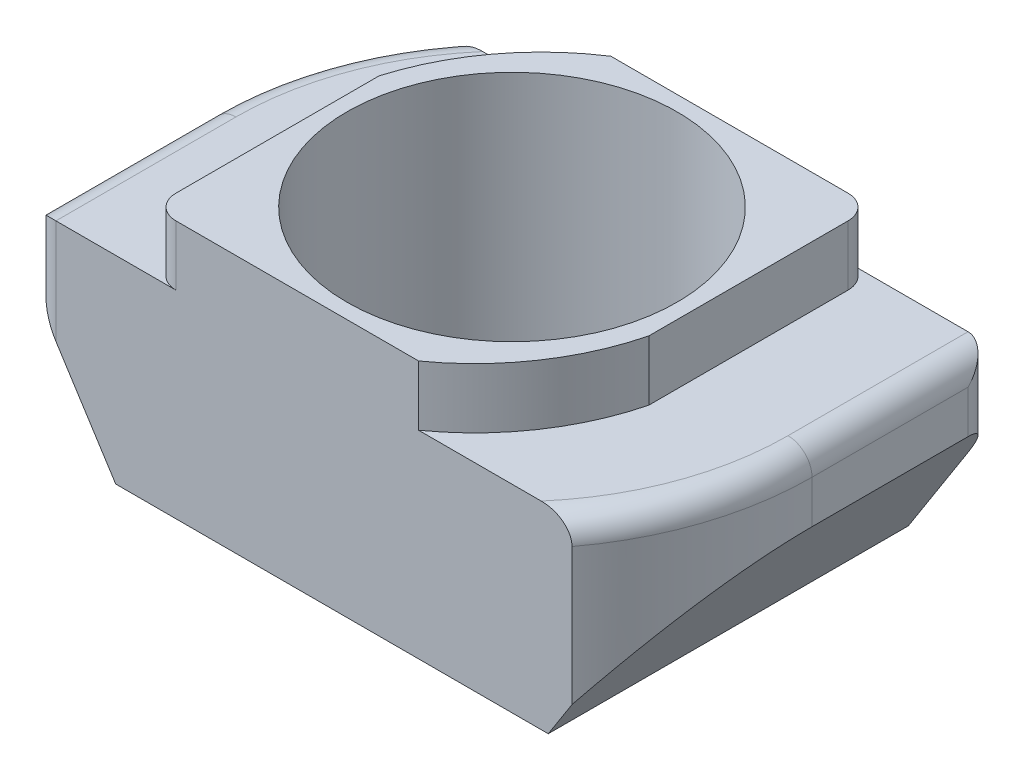
SolidWorks part; units mm, degrees
ref_plane "Front Plane" through (0, 0, 0) normal (0, 0, 1) x (1, 0, 0)
ref_plane "Top Plane" through (0, 0, 0) normal (0, 1, 0) x (1, 0, 0)
ref_plane "Right Plane" through (0, 0, 0) normal (1, 0, 0) x (0, 0, -1)
sketch "Sketch1" plane through (0, 0, 0) normal (0, 1, 0) x (1, 0, 0)
  line L1 (-5, -3) -> (4, -3)
  line L2 (-5, -3) -> (-5, 0)
  line L3 (-4, 3) -> (5, 3)
  line L4 (5, 0) -> (5, 3)
  line L5 (-5, -3) -> (5, 3) construction
  arc A0 (-4, 3) -> (-5, 0) centre (0, 0) ccw
  arc A1 (4, -3) -> (5, 0) centre (0, 0) ccw
  point P0 (0, 0)
  point P16 (0, 0)
  dimension "D4" = 5
  dimension "D1" = 10
  dimension "D2" = 6
  dimension "D3" = 2
extrude "Boss-Extrude1" add sketch "Sketch1" along normal blind 3.3
sketch "Sketch3" plane through (0, 3.3, 0) normal (0, 1, 0) x (1, 0, 0)
  line L0 (5, 3) -> (-4, 3) construction
  line L1 (-3, -3) -> (1.4435, -3)
  line L2 (-3, -3) -> (-3, 0.7854)
  line L3 (-1.3524, 3) -> (3, 3)
  line L4 (3, -0.7205) -> (3, 3)
  line L5 (-3, -3) -> (3, 3) construction
  line L6 (-2.1806, 2.2786) -> (2.1991, -2.2979) construction
  line L7 (-5, -3) -> (4, -3) construction
  arc A0 (-3, 0.7854) -> (-1.3524, 3) centre (0.836, -0.3483) cw
  arc A1 (3, -0.7205) -> (1.4435, -3) centre (-0.8788, 0.2569) cw
  point P0 (0, 0)
  point P15 (-0.0153, -0.0283)
  dimension "D2" = 4
  dimension "D1" = 6
  dimension "D3" = 2
extrude "Boss-Extrude2" add sketch "Sketch3" along normal blind 1
sketch "Sketch4" plane through (0, 4.3, 0) normal (0, 1, 0) x (1, 0, 0)
  circle A0 centre (0, 0) radius 2.75
  dimension "D1" = 5.5
extrude "Cut-Extrude1" cut sketch "Sketch4" against normal through all
sketch "Sketch5" plane through (0, 0, 3) normal (0, 0, 1) x (1, 0, 0)
  line L0 (4, 0) -> (5, 0) construction
  line L1 (5, 0) -> (5, 3.3) construction
  line L3 (-5, 0) -> (4, 0) construction
  line L9 (-5, 3.3) -> (-5, 0) construction
  line L10 (4, 0) -> (5, 0)
  line L11 (5, 0) -> (5, 2.186)
  line L13 (-5, 0) -> (-3.6042, 0)
  line L19 (-5, 2.186) -> (-5, 0)
  line L20 (-5, 2.186) -> (-3.6042, 0)
  line L21 (3.6042, 0) -> (4, 0)
  line L22 (5, 2.186) -> (3.6042, 0)
extrude "Cut-Extrude2" cut sketch "Sketch5" against normal through all
fillet "Fillet1" radius 0.4 8 edges at (5, 2.743, -3) (-5, 2.743, 3) (3, 3.8, -3) (-3, 3.8, 3) (4.7434, 3.3, 1.5811) (-4.7434, 3.3, -1.5811) (5, 3.3, -1.5) (-5, 3.3, 1.5)
